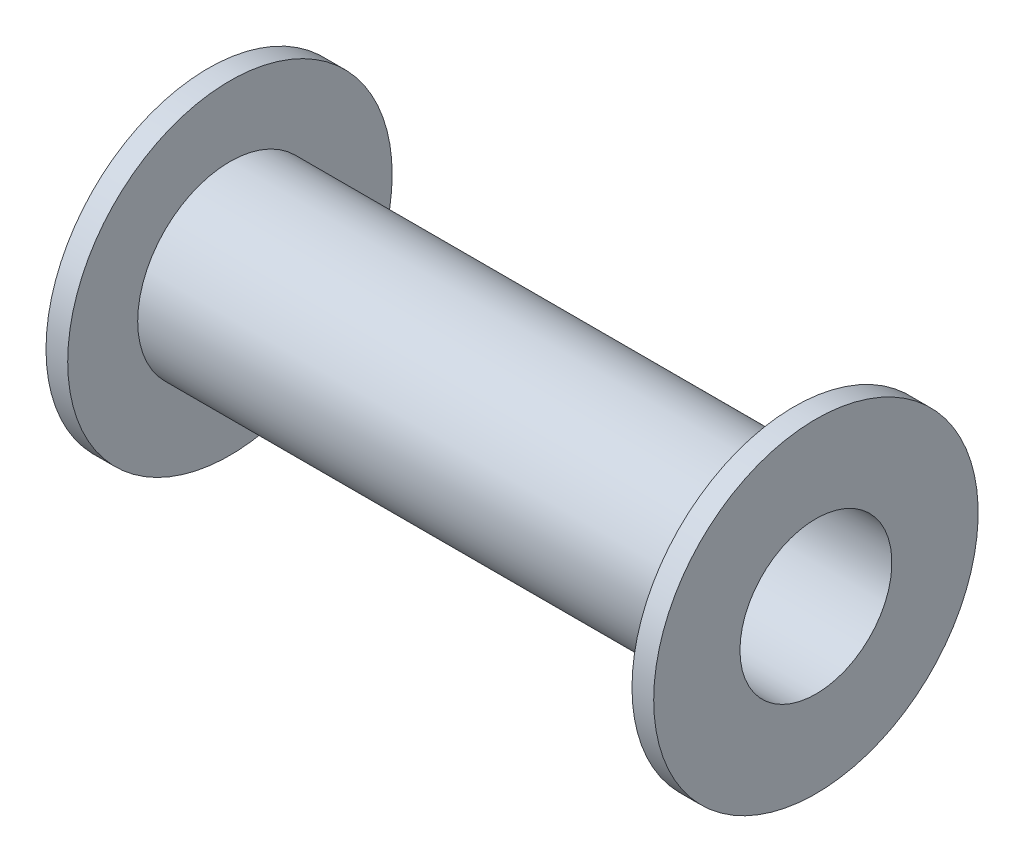
SolidWorks part; units mm, degrees
ref_plane "Plano frontal" through (0, 0, 0) normal (0, 0, 1) x (1, 0, 0)
ref_plane "Plano superior" through (0, 0, 0) normal (0, 1, 0) x (1, 0, 0)
ref_plane "Plano direito" through (0, 0, 0) normal (1, 0, 0) x (0, 0, -1)
sketch "Esboço1" plane through (0, 0, 0) normal (0, 1, 0) x (1, 0, 0)
  line L0 (-102.9595, 0) -> (95.9623, 0) construction
  line L1 (-56, -7) -> (-56, -14.95)
  line L2 (-56, -14.95) -> (-53, -14.95)
  line L3 (-53, -14.95) -> (-53, -8.5)
  line L4 (-53, -8.5) -> (-3, -8.5)
  line L5 (-3, -8.5) -> (-3, -14.95)
  line L6 (-3, -14.95) -> (0, -14.95)
  line L7 (0, -14.95) -> (0, -7)
  line L8 (-56, -7) -> (0, -7)
  dimension "D1" = 29.9
  dimension "D2" = 17
  dimension "D3" = 3
  dimension "D4" = 3
  dimension "D5" = 56
  dimension "D6" = 29.9
  dimension "D7" = 14
revolve "Revolução1" add sketch "Esboço1" angle 360 about L0
sketch "Esboço2" plane through (-53, 0, 0) normal (1, 0, 0) x (0, 0, -1)
  circle A0 centre (0, 0) radius 8.5 construction
  circle A1 centre (0, 0) radius 14.95
  circle A2 centre (0, 0) radius 14.95
  circle A3 centre (0, 0) radius 8.5
  dimension "D1" = 0
extrude "Corte-extrusão1" cut sketch "Esboço2" against normal blind 1
sketch "Esboço3" plane through (-3, 0, 0) normal (-1, 0, 0) x (0, 0, 1)
  circle A0 centre (0, 0) radius 14.95 construction
  circle A1 centre (0, 0) radius 8.5 construction
  circle A2 centre (0, 0) radius 14.95
  circle A3 centre (0, 0) radius 8.5
extrude "Corte-extrusão2" cut sketch "Esboço3" against normal blind 1
sketch "Esboço4" plane through (-54, 0, 0) normal (1, 0, 0) x (0, 0, -1)
  circle A0 centre (0, 0) radius 14.95 construction
  circle A1 centre (0, 0) radius 14.95
ref_plane "Plano1" through (-28, 0, 0) normal (-1, 0, 0) x (0, 0, 1)
